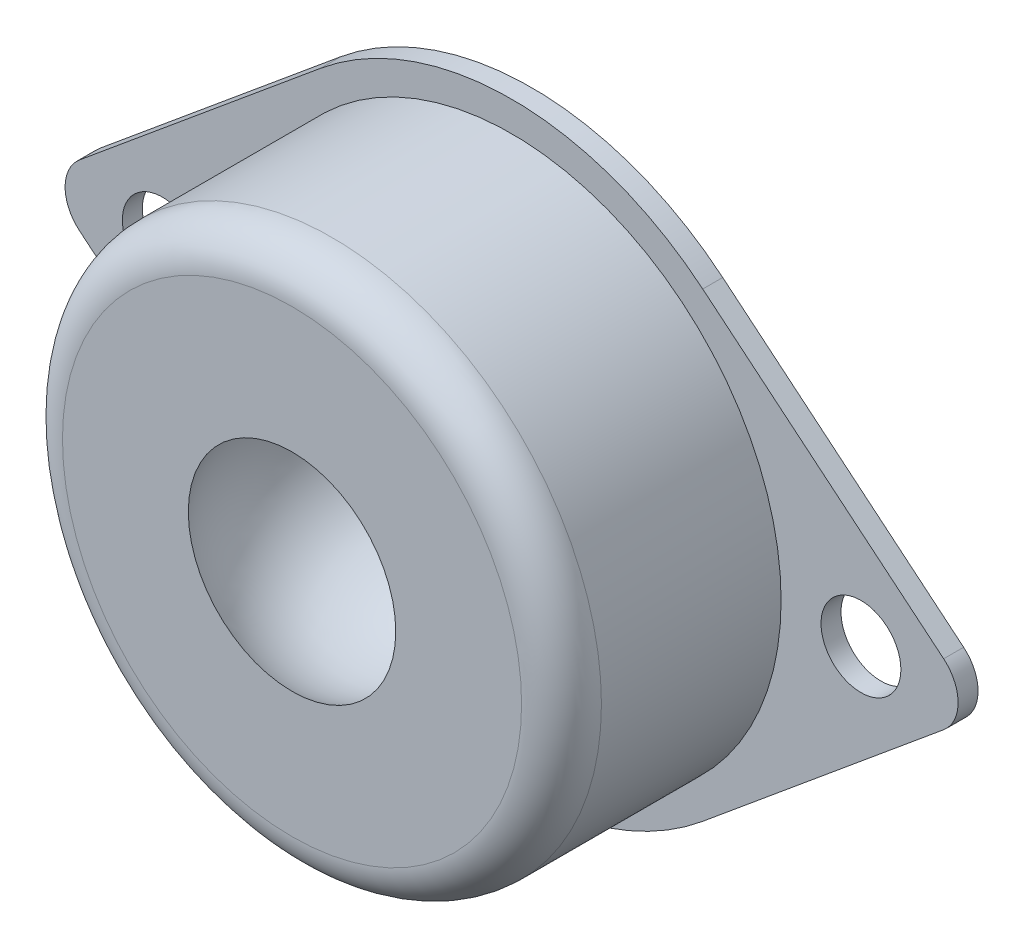
SolidWorks part; units mm, degrees
ref_plane "前视基准面" through (0, 0, 0) normal (0, 0, 1) x (1, 0, 0)
ref_plane "上视基准面" through (0, 0, 0) normal (0, 1, 0) x (1, 0, 0)
ref_plane "右视基准面" through (0, 0, 0) normal (1, 0, 0) x (0, 0, -1)
sketch "草图1" plane through (0, 0, 0) normal (0, 0, 1) x (1, 0, 0)
  line L0 (-23.5, 0) -> (23.5, 0) construction
  line L1 (0, 31.5658) -> (0, -35.7132) construction
  line L2 (-21.6433, 1.5396) -> (-9.5745, 11.5468)
  line L3 (-21.6433, -1.5396) -> (-9.5745, -11.5468)
  line L4 (21.6433, -1.5396) -> (9.5745, -11.5468)
  line L5 (21.6433, 1.5396) -> (9.5745, 11.5468)
  circle A0 centre (0, 0) radius 13.5
  circle A1 centre (-17.5, 0) radius 2
  circle A2 centre (17.5, 0) radius 2
  arc A3 (-21.6433, -1.5396) -> (-21.6433, 1.5396) centre (-20.3667, 0) cw
  arc A4 (21.6433, 1.5396) -> (21.6433, -1.5396) centre (20.3667, 0) cw
  arc A5 (-9.5745, 11.5468) -> (9.5745, 11.5468) centre (0, 0) cw
  arc A6 (-9.5745, -11.5468) -> (9.5745, -11.5468) centre (0, 0) ccw
  dimension "D1" = 27
  dimension "D4" = 2
  dimension "D5" = 2
  dimension "D6" = 4
  dimension "D7" = 15
  dimension "D2" = 47
  dimension "D3" = 35
extrude "凸台-拉伸3" add sketch "草图1" along normal blind 1 contours A3 L3 A0 L2 A1 | A4 L5 A0 L4 A2
sketch "草图3" plane through (0, 0, 0) normal (0, 0, 1) x (1, 0, 0)
  circle A0 centre (0, 0) radius 13.5
  dimension "D1" = 27
extrude "凸台-拉伸4" add sketch "草图3" along normal blind 12
fillet "圆角3" radius 2 1 edges at (13.5, 0, 12)
sketch "草图4" plane through (0, 0, 0) normal (0, 1, 0) x (1, 0, 0)
  line L1 (0, 0) -> (0, -18.0744) construction
  line L2 (0, -3) -> (0, -15) construction
  line L3 (0, -12) -> (5.1962, -12)
  line L4 (-11.5, -12) -> (11.5, -12) construction
  line L5 (0, -12) -> (0, -3)
  line L6 (9.5745, 0) -> (-9.5745, 0) construction
  circle A0 centre (0, -9) radius 6 construction
  arc A1 (0, -3) -> (0, -15) centre (0, -9) cw construction
  arc A2 (0, -3) -> (5.1962, -12) centre (0, -9) cw
  dimension "D2" = 12
  dimension "D1" = 9
revolve "切除-旋转9" cut sketch "草图4" angle 360 about L1
